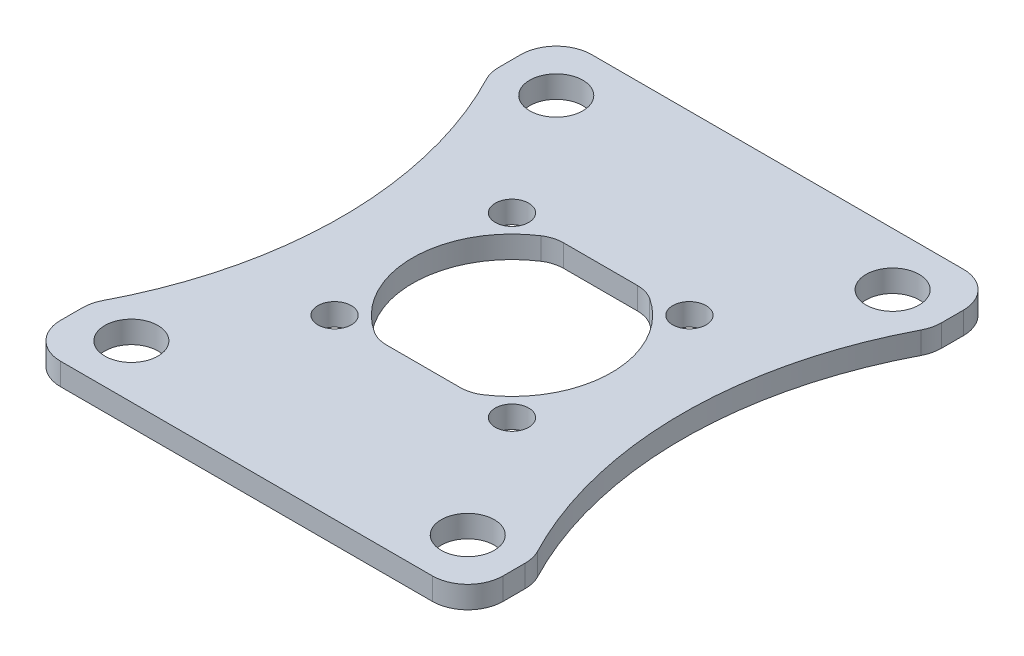
SolidWorks part; units mm, degrees
material "Alum Plate"
ref_plane "Front Plane" through (0, 0, 0) normal (0, 0, 1) x (1, 0, 0)
ref_plane "Top Plane" through (0, 0, 0) normal (0, 1, 0) x (1, 0, 0)
ref_plane "Right Plane" through (0, 0, 0) normal (1, 0, 0) x (0, 0, -1)
sketch "Sketch1" plane through (0, 0, 0) normal (0, 1, 0) x (1, 0, 0)
  line L0 (-6.364, 6.364) -> (6.364, -6.364) construction
  line L1 (-15.875, -19.05) -> (15.875, -19.05)
  line L2 (-15.875, -19.05) -> (-15.875, 19.05)
  line L3 (-15.875, 19.05) -> (15.875, 19.05)
  line L4 (15.875, -19.05) -> (15.875, 19.05)
  line L5 (-15.875, -19.05) -> (15.875, 19.05) construction
  line L6 (-15.875, 19.05) -> (15.875, -19.05) construction
  line L7 (-6.364, -6.364) -> (6.364, 6.364) construction
  line L8 (-6.364, 6.364) -> (-6.364, 19.05) construction
  line L9 (6.364, 6.364) -> (6.364, 19.05) construction
  line L10 (-15.875, 15.24) -> (-12.065, 15.24) construction
  line L11 (-12.065, 15.24) -> (-12.065, 19.05) construction
  line L12 (12.065, 19.05) -> (12.065, 15.24) construction
  line L13 (12.065, 15.24) -> (15.875, 15.24) construction
  line L14 (-12.065, 15.24) -> (0, 0) construction
  line L15 (12.065, -15.24) -> (12.065, -19.05) construction
  line L16 (12.065, -15.24) -> (15.875, -15.24) construction
  line L17 (-12.065, -19.05) -> (-12.065, -15.24) construction
  line L18 (-12.065, -15.24) -> (-15.875, -15.24) construction
  line L19 (-12.065, -15.24) -> (12.065, -15.24) construction
  circle A0 centre (0, 0) radius 7.1374
  circle A1 centre (-6.364, -6.364) radius 1.2
  circle A2 centre (-6.364, 6.364) radius 1.2
  circle A3 centre (6.364, 6.364) radius 1.2
  circle A4 centre (6.364, -6.364) radius 1.2
  circle A5 centre (-12.065, -15.24) radius 1.905
  circle A6 centre (-12.065, 15.24) radius 1.905
  circle A7 centre (12.065, 15.24) radius 1.905
  circle A8 centre (12.065, -15.24) radius 1.905
  circle A9 centre (0, 0) radius 10.9982 construction
  point P0 (0, 0)
  point P18 (0, 0)
  point P19 (0, 0)
  dimension "D1" = 14.2748
  dimension "D2" = 2.4
  dimension "D3" = 9
  dimension "D4" = 3.81
  dimension "D8" = 21.9964
  dimension "D5" = 38.1
  dimension "D6" = 31.75
  dimension "D7" = 3.81
extrude "Boss-Extrude1" add sketch "Sketch1" along normal blind 1.5875
sketch "Sketch3" plane through (0, 1.5875, 0) normal (0, 1, 0) x (1, 0, 0)
  line L0 (-3.2588, 6.35) -> (3.2588, 6.35)
  line L2 (3.2588, -6.35) -> (-3.2588, -6.35)
  arc A0 (-3.2588, -6.35) -> (3.2588, -6.35) centre (0, 0) ccw
  circle A1 centre (0, 0) radius 7.1374 construction
  arc A2 (3.2588, 6.35) -> (-3.2588, 6.35) centre (0, 0) ccw
  dimension "D1" = 12.7
extrude "Boss-Extrude3" add sketch "Sketch3" against normal through all
sketch "Sketch4" plane through (0, 0, 0) normal (0, -1, 0) x (1, 0, 0)
  line L0 (-41.9862, 0) -> (0, 0) construction
  line L1 (0, 0) -> (41.9862, 0) construction
  line L2 (-15.875, -19.05) -> (-15.875, 19.05) construction
  line L3 (15.875, 19.05) -> (15.875, -19.05) construction
  line L4 (-12.2174, 0) -> (-7.1374, 0) construction
  line L5 (-15.875, 14.2964) -> (-15.875, -14.2964)
  line L6 (15.875, -14.2964) -> (15.875, 14.2964)
  line L7 (-15.46, 13.5108) -> (-12.065, 15.24) construction
  arc A0 (-15.875, 14.2964) -> (-15.875, -14.2964) centre (-41.9862, 0) cw
  arc A1 (15.875, 14.2964) -> (15.875, -14.2964) centre (41.9862, 0) ccw
  arc A2 (-3.2588, 6.35) -> (-3.2588, -6.35) centre (0, 0) ccw construction
  dimension "D1" = 3.81
  dimension "D2" = 5.08
extrude "Cut-Extrude1" cut sketch "Sketch4" against normal through all
fillet "Fillet3" radius 2.54 8 edges at (-15.875, 0.7937, 14.2964) (-15.875, 0.7937, -14.2964) (-15.875, 0.7937, -19.05) (15.875, 0.7937, -19.05) (15.875, 0.7937, -14.2964) (15.875, 0.7937, 14.2964) (15.875, 0.7937, 19.05) (-15.875, 0.7937, 19.05)
fillet "Fillet2" radius 2.286 4 edges at (-3.2588, 0.7937, -6.35) (3.2588, 0.7937, -6.35) (3.2588, 0.7937, 6.35) (-3.2588, 0.7937, 6.35)
